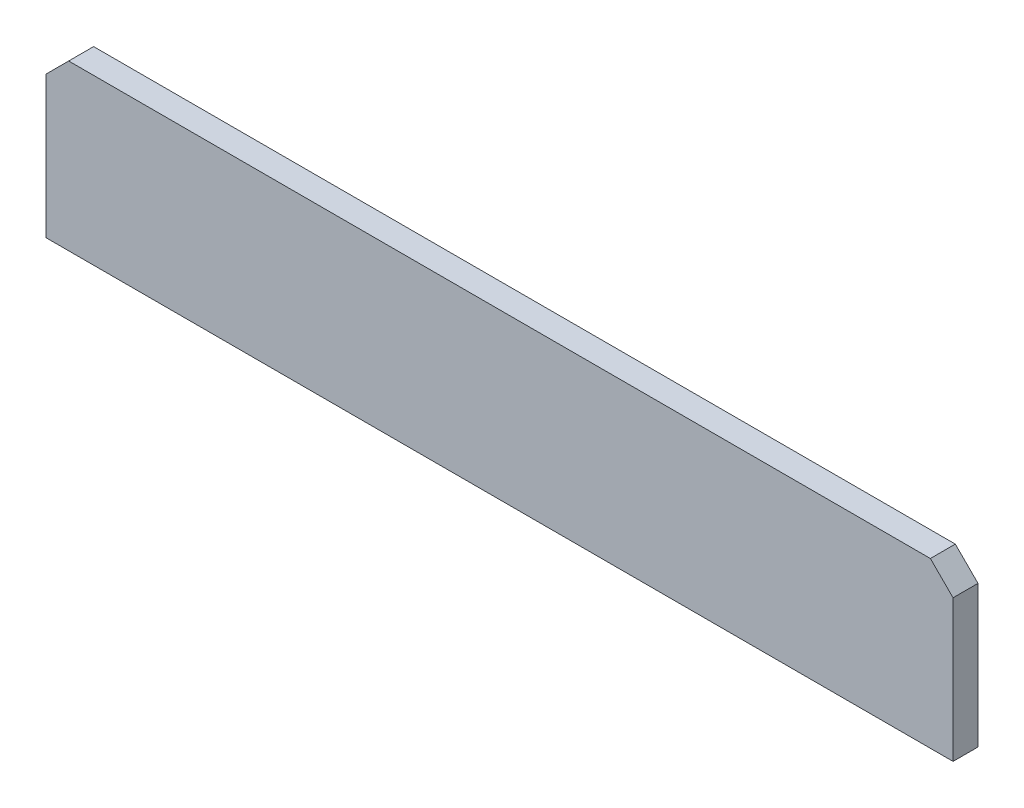
SolidWorks part; units mm, degrees
material "Pine"
ref_plane "Front Plane" through (0, 0, 0) normal (0, 0, 1) x (1, 0, 0)
ref_plane "Top Plane" through (0, 0, 0) normal (0, 1, 0) x (1, 0, 0)
ref_plane "Right Plane" through (0, 0, 0) normal (1, 0, 0) x (0, 0, -1)
sketch "Sketch1" plane through (0, 0, 0) normal (0, 0, 1) x (1, 0, 0)
  line L0 (400, -20) -> (380, 0)
  line L1 (380, 0) -> (-380, 0)
  line L2 (400, -20) -> (400, -145)
  line L3 (400, -145) -> (-400, -145)
  line L4 (-400, -20) -> (-400, -145)
  line L5 (-380, 0) -> (-400, -20)
  point P0 (400, 0)
  point P3 (-400, 0)
  point P5 (0, -145)
  dimension "D1" = 145
  dimension "D2" = 800
  dimension "D3" = 45
  dimension "D4" = 135
extrude "Boss-Extrude1" add sketch "Sketch1" along normal blind 22
